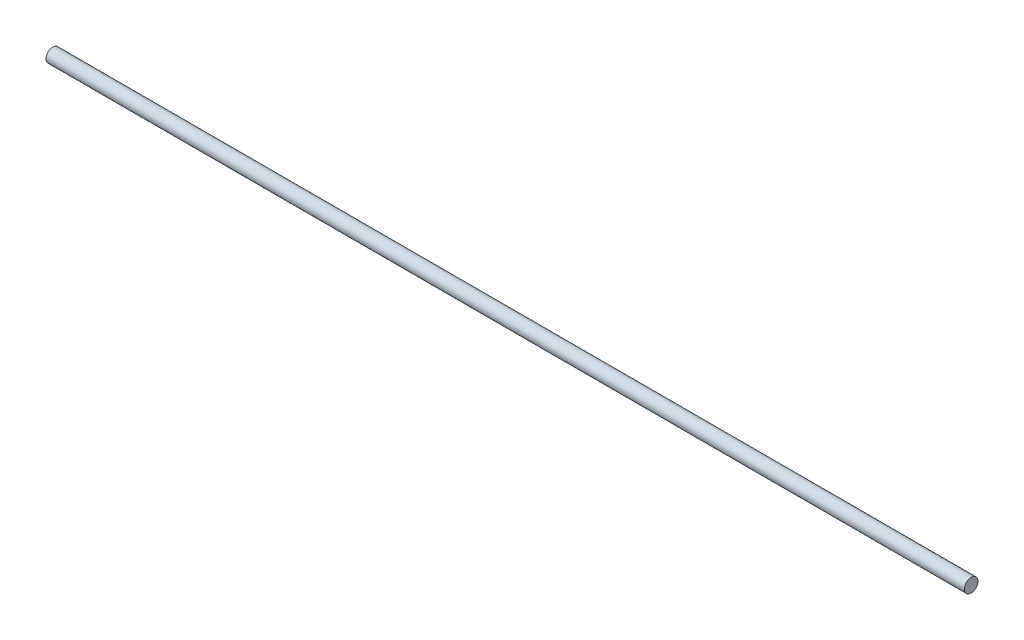
SolidWorks part; units mm, degrees
ref_plane "Front Plane" through (0, 0, 0) normal (0, 0, 1) x (1, 0, 0)
ref_plane "Top Plane" through (0, 0, 0) normal (0, 1, 0) x (1, 0, 0)
ref_plane "Right Plane" through (0, 0, 0) normal (1, 0, 0) x (0, 0, -1)
sketch "Sketch1" plane through (0, 0, 0) normal (0, 0, 1) x (1, 0, 0)
  line L0 (2.327, -15.7794) -> (14.6716, 9.7434) construction
  line L1 (14.6716, 9.7434) -> (-294.9694, 9.7434) construction
  line L2 (-294.9694, 9.7434) -> (2.327, -15.7794) construction
  line L3 (14.6716, 9.7434) -> (-34.0167, 9.7434) construction
  line L4 (8.9053, 11.7434) -> (-34.0167, 11.7434) construction
  line L5 (8.9053, 7.7434) -> (11.4958, 7.7434) construction
  line L6 (14.6716, 11.7434) -> (-34.0167, 11.7434) construction
  line L7 (8.9053, 11.7434) -> (8.9053, 9.7434) construction
  line L8 (-294.9694, 9.7434) -> (-279.9694, 9.7434) construction
  line L9 (-34.0167, 11.7434) -> (-34.0167, 7.7434) construction
  line L10 (0.7856, -13.8112) -> (6.2479, 6.4835) construction
  line L11 (5.2823, 7.7434) -> (-34.0167, 7.7434) construction
  line L12 (14.6716, 7.7434) -> (-34.0167, 7.7434) construction
  line L13 (4.6481, -14.8508) -> (10.5302, 7.0033) construction
  line L14 (-9.3284, 9.7434) -> (14.6716, 9.7434)
  circle A0 centre (2.327, -15.7794) radius 1 construction
  circle A1 centre (14.6716, 9.7434) radius 3 construction
  arc A2 (9.7924, 7.2049) -> (9.7924, 12.2819) centre (14.6716, 9.7434) ccw construction
  arc A3 (0.7856, -13.8112) -> (4.6481, -14.8508) centre (2.327, -15.7794) ccw construction
  arc A4 (5.2823, 7.7434) -> (6.2479, 6.4835) centre (5.2823, 6.7434) cw construction
  arc A5 (10.5302, 7.0033) -> (11.4958, 7.7434) centre (11.4958, 6.7434) cw construction
  arc A6 (9.7924, 7.2049) -> (8.9053, 7.7434) centre (8.9053, 6.7434) ccw construction
  arc A7 (9.7924, 12.2819) -> (8.9053, 11.7434) centre (8.9053, 12.7434) cw construction
  circle A8 centre (-294.9694, 9.7434) radius 15 construction
  circle A9 centre (14.6716, 9.7434) radius 24
  dimension "D1" = 28.3514
  dimension "D4" = 2
  dimension "D6" = 1
  dimension "D7" = 1
  dimension "D8" = 1
  dimension "D9" = 1
  dimension "D10" = 2.5
  dimension "D11" = 2
  dimension "D13" = 5.5
  dimension "D14" = 6
  dimension "D2" = 309.641
  dimension "D3" = 298.39
  dimension "D12" = 4
  dimension "D5" = 2
sketch "Sketch3" plane through (0, 0, 0) normal (1, 0, 0) x (0, 0, -1)
  line L0 (0, 24.7434) -> (0, -5.2566) construction
  circle A0 centre (0, 9.7434) radius 2
extrude "Boss-Extrude1" add sketch "Sketch3" against normal up to vertex (279.9694 mm away) from vertex at -9.3284 separate body starting at point (-9.3284, 9.7434, 0)
